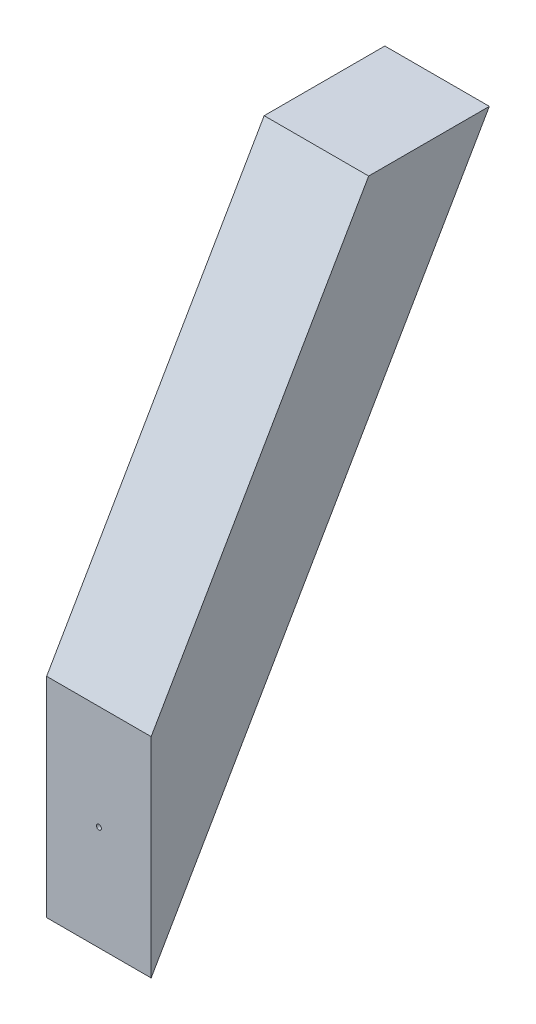
SolidWorks part; units mm, degrees
ref_plane "Front Plane" through (0, 0, 0) normal (0, 0, 1) x (1, 0, 0)
ref_plane "Top Plane" through (0, 0, 0) normal (0, 1, 0) x (1, 0, 0)
ref_plane "Right Plane" through (0, 0, 0) normal (1, 0, 0) x (0, 0, -1)
sketch "Sketch1" plane through (0, 0, 0) normal (1, 0, 0) x (0, 0, -1)
  line L0 (0, 0) -> (0, 50.8)
  line L1 (0, 50.8) -> (52.861, 142.3579)
  line L2 (52.861, 142.3579) -> (82.1904, 142.3579)
  line L3 (82.1904, 142.3579) -> (0, 0)
  dimension "D1" = 25.4
  dimension "D2" = 105.722
  dimension "D3" = 30
extrude "Boss-Extrude1" add sketch "Sketch1" along normal mid plane 25.4
hole_wizard "#0-80 Tapped Hole1" positions "Sketch4" profile "Sketch3" tap size "#0-80" standard "ANSI Inch"
sketch "Sketch4" plane through (0, 0, 0) normal (0, 0, 1) x (1, 0, 0)
  line L0 (0, 0) -> (0, 50.8) construction
  line L1 (12.7, 0) -> (-12.7, 0) construction
  line L2 (12.7, 50.8) -> (-12.7, 50.8) construction
  line L4 (-12.7, 25.4) -> (12.7, 25.4) construction
  line L5 (-12.7, 50.8) -> (-12.7, 0) construction
  line L6 (12.7, 50.8) -> (12.7, 0) construction
  point P0 (0, 25.4)
  point P20 (0, 25.4)
sketch "Sketch3" plane through (0, 25.4, 0) normal (1, 0, 0) x (0, -1, 0)
  line L0 (0, 0) -> (0, 10.3579)
  line L1 (0, 10.3579) -> (0.5956, 10)
  line L2 (0.5956, 10) -> (0.5956, 0)
  line L5 (0.5956, 0) -> (0, 0)
  line L10 (0, 10.3579) -> (-0.5956, 10) construction
  line L11 (0, -6.35) -> (0, 107.95) construction
  dimension "Tap Drill Dia." = 1.1913
  dimension "Tap Drill Depth" = 10
  dimension "Drill Angle" = 118
ref_plane "Plane1" through (0, 35.5895, -61.6428) normal (0, -0.5, 0.866) x (-1, 0, 0)
